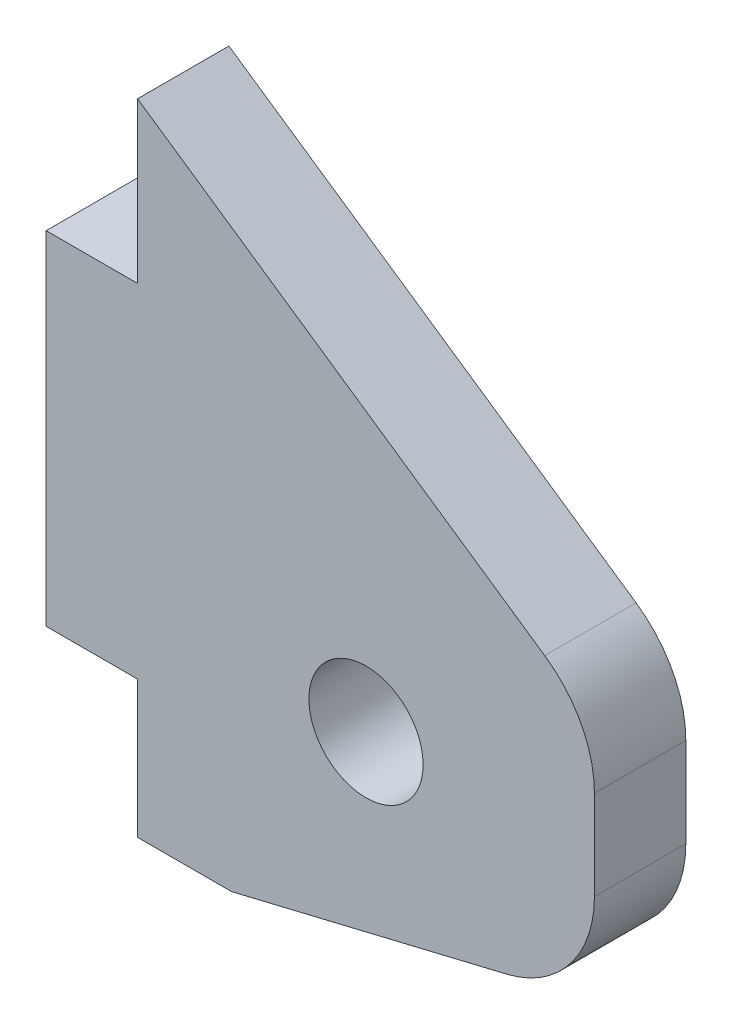
SolidWorks part; units mm, degrees
material "ﾊﾞﾙｻ"
ref_plane "正面" through (0, 0, 0) normal (0, 0, 1) x (1, 0, 0)
ref_plane "平面" through (0, 0, 0) normal (0, 1, 0) x (1, 0, 0)
ref_plane "右側面" through (0, 0, 0) normal (1, 0, 0) x (0, 0, -1)
sketch "ｽｹｯﾁ1" plane through (0, 0, 0) normal (0, 0, 1) x (1, 0, 0)
  line L0 (0, 0) -> (0, 15)
  line L1 (0, 15) -> (4, 15)
  line L2 (4, 15) -> (4, 22)
  line L3 (4, 22) -> (24, 22)
  line L4 (24, 22) -> (24, -6)
  line L5 (24, -6) -> (4, -6)
  line L6 (4, -6) -> (4, 0)
  line L7 (4, 0) -> (0, 0)
  line L8 (14, 22) -> (14, -6) construction
  line L9 (4, 22) -> (24, 8.3124)
  line L10 (8.1108, -6) -> (24, -2.1832)
  circle A0 centre (14, 3) radius 2.5
  dimension "D6" = 5
  dimension "D7" = 9
  dimension "D1" = 15
  dimension "D2" = 6
  dimension "D3" = 7
  dimension "D4" = 4
  dimension "D5" = 20
extrude "ﾎﾞｽ - 押し出し1" add sketch "ｽｹｯﾁ1" along normal blind 4 contours L5 L10 L4 L3 L2 L1 L0 L7 L6 A0 | L9 L8 A0 L10 L4
fillet "ﾌｨﾚｯﾄ1" radius 5 2 edges at (24, 8.3124, 2) (24, -2.1832, 2)
